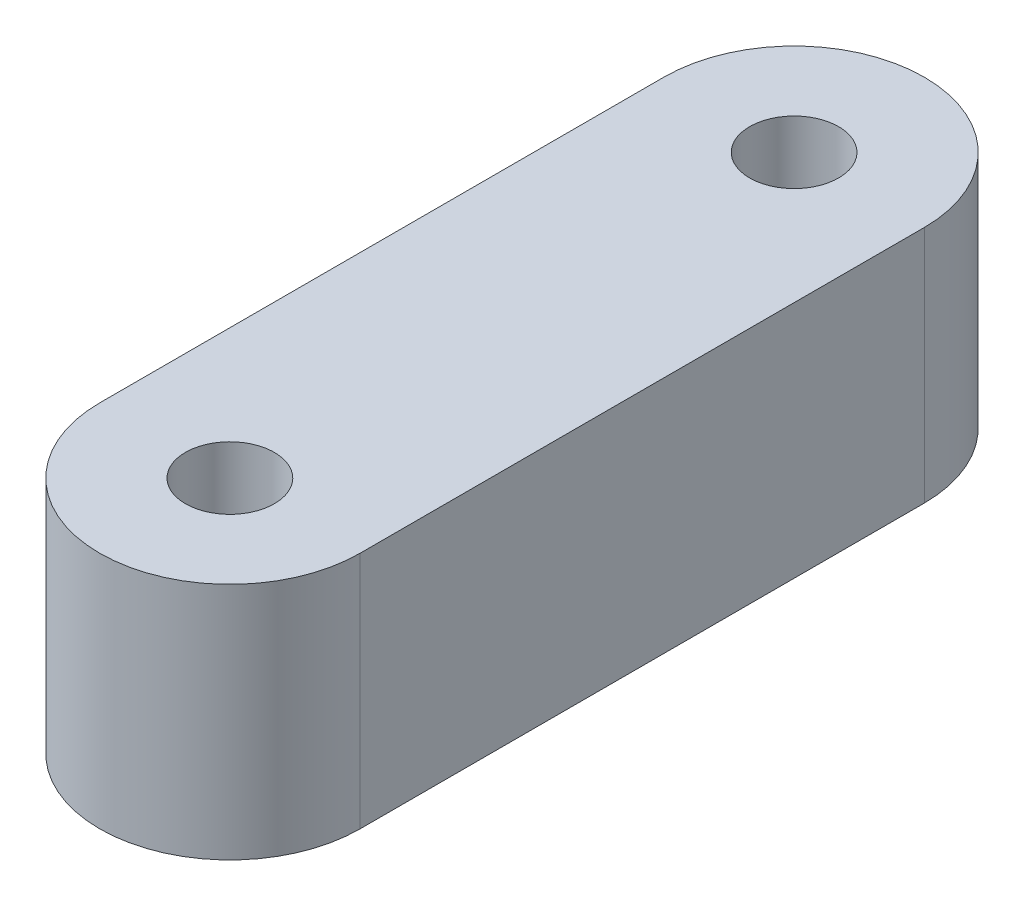
SolidWorks part; units mm, degrees
ref_plane "前视基准面" through (0, 0, 0) normal (0, 0, 1) x (1, 0, 0)
ref_plane "上视基准面" through (0, 0, 0) normal (0, 1, 0) x (1, 0, 0)
ref_plane "右视基准面" through (0, 0, 0) normal (1, 0, 0) x (0, 0, -1)
sketch "草图1" plane through (0, 0, 0) normal (0, 1, 0) x (1, 0, 0)
  line L0 (0, -13) -> (0, 13) construction
  line L1 (-6, -13) -> (-6, 13)
  line L2 (6, -13) -> (6, 13)
  arc A0 (-6, -13) -> (6, -13) centre (0, -13) ccw
  arc A1 (6, 13) -> (-6, 13) centre (0, 13) ccw
  point P2 (0, 0)
  dimension "D1" = 26
  dimension "D2" = 12
extrude "凸台-拉伸1" add sketch "草图1" along normal blind 11
sketch "草图2" plane through (0, 11, 0) normal (0, 1, 0) x (1, 0, 0)
  circle A0 centre (0, 13) radius 2.05
  circle A1 centre (0, -13) radius 2.05
  dimension "D1" = 13
  dimension "D3" = 4.1
  dimension "D4" = 4.1
  dimension "D5" = 0
  dimension "D6" = 0
  dimension "D2" = 13
extrude "切除-拉伸1" cut sketch "草图2" against normal through all
sketch "草图3" plane through (-6, 0, 0) normal (-1, 0, 0) x (0, 0, 1)
  line L0 (-13, 0) -> (13, 0) construction
  circle A0 centre (0, 5.5) radius 3.1
  dimension "D1" = 5.5
  dimension "D2" = 6.2
extrude "切除-拉伸2" cut sketch "草图3" against normal blind 10
sketch "草图4" plane through (-6, 0, 0) normal (-1, 0, 0) x (0, 0, 1)
  line L1 (-5, -3.75) -> (5, -3.75)
  line L2 (-5, -3.75) -> (-5, 3.75)
  line L3 (-5, 3.75) -> (5, 3.75)
  line L4 (5, -3.75) -> (5, 3.75)
  line L5 (-5, -3.75) -> (5, 3.75) construction
  line L6 (-5, 3.75) -> (5, -3.75) construction
  circle A0 centre (0, 5.5) radius 3.6
  point P3 (0, 0)
  circle M5 centre (0, 5.5) radius 3.1
  dimension "D1" = 10
  dimension "D2" = 1.75
extrude "凸台-拉伸3" add sketch "草图4" against normal blind 10 contours L3 M5
